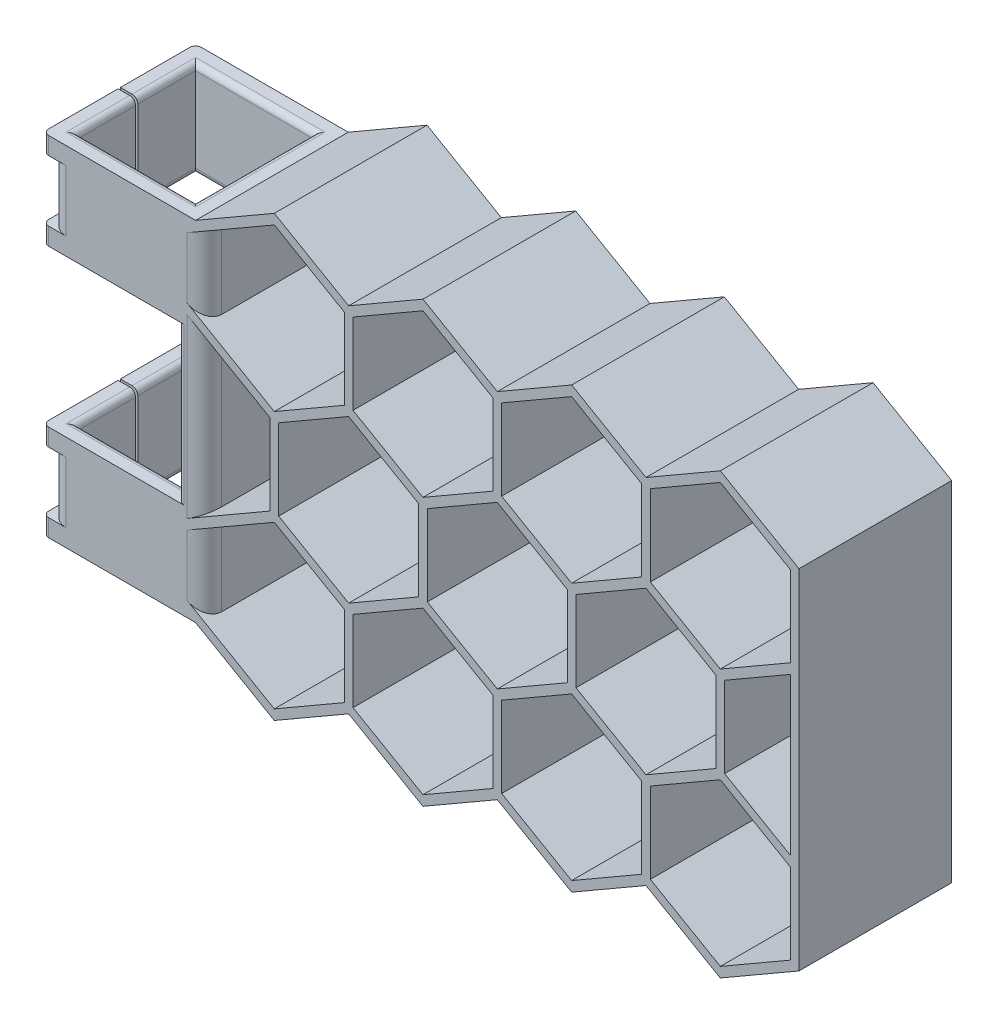
SolidWorks part; units mm, degrees
ref_plane "Front Plane" through (0, 0, 0) normal (0, 0, 1) x (1, 0, 0)
ref_plane "Top Plane" through (0, 0, 0) normal (0, 1, 0) x (1, 0, 0)
ref_plane "Right Plane" through (0, 0, 0) normal (1, 0, 0) x (0, 0, -1)
sketch "Sketch1" plane through (0, 0, 0) normal (0, 1, 0) x (1, 0, 0)
  line L1 (0, 0) -> (20.3, 0)
  line L2 (0, 0) -> (0, 20.3)
  line L3 (0, 20.3) -> (20.3, 20.3)
  line L4 (20.3, 0) -> (20.3, 20.3)
  line L5 (-3, -3) -> (23.3, -3)
  line L6 (-3, -3) -> (-3, 23.3)
  line L7 (-3, 23.3) -> (23.3, 23.3)
  line L8 (23.3, -3) -> (23.3, 23.3)
  line L9 (20.3, 20.3) -> (23.3, 20.3) construction
  line L10 (20.3, 20.3) -> (20.3, 23.3) construction
  line L11 (20.3, 23.3) -> (23.3, 23.3) construction
  line L12 (23.3, 20.3) -> (23.3, 23.3) construction
  line L13 (0, 0) -> (-3, 0) construction
  line L14 (0, 0) -> (0, -3) construction
  line L15 (0, -3) -> (-3, -3) construction
  line L16 (-3, 0) -> (-3, -3) construction
  dimension "D1" = 20.3
  dimension "D2" = 3
extrude "Tube Extrude" add sketch "Sketch1" along normal blind 60
ref_plane "tube outer plane" through (0, 0, 3) normal (0, 0, 1) x (1, 0, 0)
sketch "Sketch2" plane through (0, 0, 3) normal (0, 0, 1) x (1, 0, 0)
  line L0 (23.3, 60) -> (23.3, 0) construction
  line L1 (49.6558, 16.0825) -> (37.6029, 23.0413)
  line L2 (36.1029, 23.0413) -> (24.8, 16.5155)
  line L3 (23.3, 15.6495) -> (23.3, 0)
  line L4 (23.3, 0) -> (36.8529, -7.8248)
  line L5 (36.8529, -7.8248) -> (49.6558, -0.433)
  line L6 (50.4058, 0.866) -> (50.4058, 14.7835) construction
  line L7 (75.2615, 16.0825) -> (62.4586, 23.4743) construction
  line L8 (24.8, 0.866) -> (36.8529, -6.0927)
  line L9 (36.8529, -6.0927) -> (48.9058, 0.866)
  line L10 (48.9058, 0.866) -> (48.9058, 14.7835)
  line L11 (48.9058, 14.7835) -> (36.8529, 21.7422)
  line L12 (36.8529, 21.7422) -> (24.8, 14.7835)
  line L13 (24.8, 14.7835) -> (24.8, 0.866)
  line L14 (62.4586, 23.4743) -> (49.6558, 16.0825) construction
  line L15 (48.9058, 14.7835) -> (48.9058, 0.866) construction
  line L16 (49.6558, -0.433) -> (62.4586, -7.8248)
  line L17 (62.4586, -7.8248) -> (75.2615, -0.433)
  line L18 (76.0115, 0.866) -> (76.0115, 14.7835) construction
  line L19 (50.4058, 0.866) -> (62.4586, -6.0927)
  line L20 (62.4586, -6.0927) -> (74.5115, 0.866)
  line L21 (74.5115, 0.866) -> (74.5115, 14.7835)
  line L22 (74.5115, 14.7835) -> (62.4586, 21.7422)
  line L23 (62.4586, 21.7422) -> (50.4058, 14.7835)
  line L24 (50.4058, 14.7835) -> (50.4058, 0.866)
  line L25 (100.8673, 16.0825) -> (88.0644, 23.4743) construction
  line L26 (88.0644, 23.4743) -> (75.2615, 16.0825) construction
  line L27 (74.5115, 14.7835) -> (74.5115, 0.866) construction
  line L28 (75.2615, -0.433) -> (88.0644, -7.8248)
  line L29 (88.0644, -7.8248) -> (100.8673, -0.433)
  line L30 (101.6173, 0.866) -> (101.6173, 14.7835) construction
  line L31 (76.0115, 0.866) -> (88.0644, -6.0927)
  line L32 (88.0644, -6.0927) -> (100.1173, 0.866)
  line L33 (100.1173, 0.866) -> (100.1173, 14.7835)
  line L34 (100.1173, 14.7835) -> (88.0644, 21.7422)
  line L35 (88.0644, 21.7422) -> (76.0115, 14.7835)
  line L36 (76.0115, 14.7835) -> (76.0115, 0.866)
  line L37 (125.723, 16.5155) -> (114.4202, 23.0413)
  line L38 (112.9202, 23.0413) -> (100.8673, 16.0825) construction
  line L39 (100.1173, 14.7835) -> (100.1173, 0.866) construction
  line L40 (100.8673, -0.433) -> (113.6702, -7.8248)
  line L41 (113.6702, -7.8248) -> (127.223, 0)
  line L42 (127.223, 0) -> (127.223, 15.6495)
  line L43 (101.6173, 0.866) -> (113.6702, -6.0927)
  line L44 (113.6702, -6.0927) -> (125.723, 0.866)
  line L45 (125.723, 0.866) -> (125.723, 14.7835)
  line L46 (125.723, 14.7835) -> (113.6702, 21.7422)
  line L47 (113.6702, 21.7422) -> (101.6173, 14.7835)
  line L48 (101.6173, 14.7835) -> (101.6173, 0.866)
  line L85 (49.6558, 60.433) -> (36.8529, 67.8248)
  line L86 (36.8529, 67.8248) -> (23.3, 60)
  line L87 (23.3, 60) -> (23.3, 44.3505)
  line L88 (24.8, 43.4845) -> (36.1029, 36.9587)
  line L89 (37.6029, 36.9587) -> (49.6558, 43.9175) construction
  line L90 (75.2615, 60.433) -> (62.4586, 67.8248)
  line L91 (24.8, 45.2165) -> (36.8529, 38.2578)
  line L92 (36.8529, 38.2578) -> (48.9058, 45.2165)
  line L93 (48.9058, 45.2165) -> (48.9058, 59.134)
  line L94 (48.9058, 59.134) -> (36.8529, 66.0927)
  line L95 (36.8529, 66.0927) -> (24.8, 59.134)
  line L96 (24.8, 59.134) -> (24.8, 45.2165)
  line L97 (62.4586, 67.8248) -> (49.6558, 60.433)
  line L98 (49.6558, 43.9175) -> (62.4586, 36.5257) construction
  line L99 (62.4586, 36.5257) -> (75.2615, 43.9175) construction
  line L100 (50.4058, 45.2165) -> (62.4586, 38.2578)
  line L101 (62.4586, 38.2578) -> (74.5115, 45.2165)
  line L102 (74.5115, 45.2165) -> (74.5115, 59.134)
  line L103 (74.5115, 59.134) -> (62.4586, 66.0927)
  line L104 (62.4586, 66.0927) -> (50.4058, 59.134)
  line L105 (50.4058, 59.134) -> (50.4058, 45.2165)
  line L106 (100.8673, 60.433) -> (88.0644, 67.8248)
  line L107 (88.0644, 67.8248) -> (75.2615, 60.433)
  line L108 (75.2615, 43.9175) -> (88.0644, 36.5257) construction
  line L109 (88.0644, 36.5257) -> (100.8673, 43.9175) construction
  line L110 (76.0115, 45.2165) -> (88.0644, 38.2578)
  line L111 (88.0644, 38.2578) -> (100.1173, 45.2165)
  line L112 (100.1173, 45.2165) -> (100.1173, 59.134)
  line L113 (100.1173, 59.134) -> (88.0644, 66.0927)
  line L114 (88.0644, 66.0927) -> (76.0115, 59.134)
  line L115 (76.0115, 59.134) -> (76.0115, 45.2165)
  line L116 (127.223, 60) -> (113.6702, 67.8248)
  line L117 (113.6702, 67.8248) -> (100.8673, 60.433)
  line L118 (100.8673, 43.9175) -> (113.6702, 36.5257) construction
  line L119 (114.4202, 36.9587) -> (125.723, 43.4845)
  line L120 (127.223, 44.3505) -> (127.223, 60)
  line L121 (101.6173, 45.2165) -> (113.6702, 38.2578)
  line L122 (113.6702, 38.2578) -> (125.723, 45.2165)
  line L123 (125.723, 45.2165) -> (125.723, 59.134)
  line L124 (125.723, 59.134) -> (113.6702, 66.0927)
  line L125 (113.6702, 66.0927) -> (101.6173, 59.134)
  line L126 (101.6173, 59.134) -> (101.6173, 45.2165)
  line L127 (50.4058, 45.2165) -> (50.4058, 59.134) construction
  line L128 (48.9058, 59.134) -> (48.9058, 45.2165) construction
  line L129 (76.0115, 45.2165) -> (76.0115, 59.134) construction
  line L130 (74.5115, 59.134) -> (74.5115, 45.2165) construction
  line L131 (101.6173, 45.2165) -> (101.6173, 59.134) construction
  line L132 (100.1173, 59.134) -> (100.1173, 45.2165) construction
  line L133 (114.4202, 23.0413) -> (114.4202, 22.1752) construction
  line L134 (62.4586, 21.7422) -> (75.2615, 14.3505) construction
  line L135 (36.8529, 21.7422) -> (49.6558, 14.3505) construction
  line L136 (49.6558, 14.3505) -> (62.4586, 21.7422) construction
  line L137 (63.2086, 23.0413) -> (63.2086, 36.9587) construction
  line L138 (62.4586, 38.2578) -> (49.6558, 45.6495) construction
  line L139 (49.6558, 45.6495) -> (36.8529, 38.2578) construction
  line L140 (36.1029, 36.9587) -> (36.1029, 23.0413)
  line L141 (49.6558, 16.0825) -> (61.7086, 23.0413)
  line L142 (61.7086, 23.0413) -> (61.7086, 36.9587)
  line L143 (61.7086, 36.9587) -> (49.6558, 43.9175)
  line L144 (49.6558, 43.9175) -> (37.6029, 36.9587)
  line L145 (37.6029, 36.9587) -> (37.6029, 23.0413)
  line L146 (37.6029, 23.0413) -> (49.6558, 16.0825)
  line L147 (75.2615, 14.3505) -> (88.0644, 21.7422) construction
  line L148 (88.8144, 23.0413) -> (88.8144, 36.9587) construction
  line L149 (88.0644, 38.2578) -> (75.2615, 45.6495) construction
  line L150 (75.2615, 45.6495) -> (62.4586, 38.2578) construction
  line L151 (61.7086, 36.9587) -> (61.7086, 23.0413) construction
  line L152 (75.2615, 16.0825) -> (87.3144, 23.0413)
  line L153 (87.3144, 23.0413) -> (87.3144, 36.9587)
  line L154 (87.3144, 36.9587) -> (75.2615, 43.9175)
  line L155 (75.2615, 43.9175) -> (63.2086, 36.9587)
  line L156 (63.2086, 36.9587) -> (63.2086, 23.0413)
  line L157 (63.2086, 23.0413) -> (75.2615, 16.0825)
  line L158 (88.0644, 21.7422) -> (100.8673, 14.3505) construction
  line L159 (100.8673, 14.3505) -> (114.4202, 22.1752) construction
  line L160 (114.4202, 23.0413) -> (114.4202, 36.9587)
  line L161 (113.6702, 38.2578) -> (100.8673, 45.6495) construction
  line L162 (100.8673, 45.6495) -> (88.0644, 38.2578) construction
  line L163 (87.3144, 36.9587) -> (87.3144, 23.0413) construction
  line L164 (100.8673, 16.0825) -> (112.9202, 23.0413)
  line L165 (112.9202, 23.0413) -> (112.9202, 36.9587)
  line L166 (112.9202, 36.9587) -> (100.8673, 43.9175)
  line L167 (100.8673, 43.9175) -> (88.8144, 36.9587)
  line L168 (88.8144, 36.9587) -> (88.8144, 23.0413)
  line L169 (88.8144, 23.0413) -> (100.8673, 16.0825)
  line L170 (114.4202, 36.9587) -> (113.6702, 36.5257)
  line L171 (127.223, 44.3505) -> (127.223, 15.6495)
  line L172 (125.723, 16.5155) -> (125.723, 43.4845)
  line L173 (23.3, 15.6495) -> (23.3, 44.3505)
  line L174 (24.8, 16.5155) -> (24.8, 43.4845)
  line L180 (-3, 60) -> (23.3, 60) construction
  circle A0 centre (36.8529, 7.8248) radius 13.5529 construction
  circle A1 centre (36.8529, 7.8248) radius 12.0529 construction
  circle A2 centre (62.4586, 7.8248) radius 13.5529 construction
  circle A3 centre (62.4586, 7.8248) radius 12.0529 construction
  circle A4 centre (88.0644, 7.8248) radius 13.5529 construction
  circle A5 centre (88.0644, 7.8248) radius 12.0529 construction
  circle A6 centre (113.6702, 7.8248) radius 13.5529 construction
  circle A7 centre (113.6702, 7.8248) radius 12.0529 construction
  circle A8 centre (49.6558, 30) radius 13.5529 construction
  circle A9 centre (49.6558, 30) radius 12.0529 construction
  circle A10 centre (75.2615, 30) radius 13.5529 construction
  circle A11 centre (75.2615, 30) radius 12.0529 construction
  circle A12 centre (100.8673, 30) radius 13.5529 construction
  circle A13 centre (100.8673, 30) radius 12.0529 construction
  circle A14 centre (36.8529, 52.1752) radius 13.5529 construction
  circle A15 centre (36.8529, 52.1752) radius 12.0529 construction
  circle A16 centre (62.4586, 52.1752) radius 13.5529 construction
  circle A17 centre (62.4586, 52.1752) radius 12.0529 construction
  circle A18 centre (88.0644, 52.1752) radius 13.5529 construction
  circle A19 centre (88.0644, 52.1752) radius 12.0529 construction
  circle A20 centre (113.6702, 52.1752) radius 13.5529 construction
  circle A21 centre (113.6702, 52.1752) radius 12.0529 construction
  dimension "D1" = 0
  dimension "D2" = 1.5
  dimension "D3" = 4
  dimension "D5" = 2
  dimension "D4" = 3
extrude "Hex Extrude" add sketch "Sketch2" against normal up to surface (26.3 mm away) contours L12 L13 L8 L9 L10 L11 | L23 L24 L19 L20 L21 L22 | L144 L145 L1 L141 L142 L143 | L174 L2 L140 L88 | L95 L96 L91 L92 L93 L94 | L104 L105 L100 L101 L102 L103 | L156 L157 L152 L153 L154 L155 | L35 L36 L31 L32 L33 L34 | L168 L169 L164 L165 L166 L167 | L114 L115 L110 L111 L112 L113 | L125 L126 L121 L122 L123 L124 | L47 L48 L43 L44 L45 L46 | L37 L172 L119 L160 | L16 L17 L28 L29 L40 L41 L42 L171 L120 L116 L117 L106 L107 L90 L97 L85 L86 L87 L173 L3 L4 L5
sketch "Sketch3" plane through (0, 0, 3) normal (0, 0, 1) x (1, 0, 0)
  line L0 (-3, 60) -> (-3, 0) construction
  line L1 (20.3, 43.4845) -> (-3, 43.4845)
  line L2 (20.3, 43.4845) -> (20.3, 16.5155)
  line L3 (20.3, 16.5155) -> (-3, 16.5155)
  line L4 (-3, 43.4845) -> (-3, 16.5155)
  line L5 (20.3, 43.4845) -> (24.8, 43.4845) construction
  line L6 (20.3, 16.5155) -> (24.8, 16.5155) construction
extrude "Tube Center Cut" cut sketch "Sketch3" against normal through all both and the other way through all
ref_plane "Plane1" through (-3, 0, 0) normal (-1, 0, 0) x (0, 0, 1)
sketch "Sketch4" plane through (-3, 0, 0) normal (-1, 0, 0) x (0, 0, 1)
  line L0 (-10.15, 60) -> (-10.35, 60)
  line L1 (-23.3, 60) -> (3, 60) construction
  line L2 (-10.35, 60) -> (-10.35, 0)
  line L3 (-23.3, 0) -> (3, 0) construction
  line L4 (-10.35, 0) -> (-10.15, 0)
  line L5 (-10.15, 0) -> (-9.95, 0)
  line L6 (-9.95, 0) -> (-9.95, 60)
  line L7 (-9.95, 60) -> (-10.15, 60)
  dimension "D1" = 0.2
extrude "Cut-Extrude1" cut sketch "Sketch4" against normal up to next
sketch "Sketch5" plane through (0, 0, 3) normal (0, 0, 1) x (1, 0, 0)
  line L0 (-3, 7.1225) -> (-3, -7.1225) construction
  line L1 (-3, 57) -> (-2, 57)
  line L2 (-3, 57) -> (-3, 46.4845)
  line L3 (-3, 46.4845) -> (-2, 46.4845)
  line L4 (-2, 57) -> (-2, 46.4845)
  line L5 (20.3, 30) -> (-9.7, 30) construction
  line L6 (20.3, 43.4845) -> (20.3, 16.5155) construction
  line L7 (-2, 57) -> (-2, 60) construction
  line L8 (-3, 60) -> (23.3, 60) construction
  line L9 (-2, 46.4845) -> (-2, 43.4845) construction
  line L10 (-3, 43.4845) -> (20.3, 43.4845) construction
  line L11 (-2, 3) -> (-2, 13.5155)
  line L12 (-3, 13.5155) -> (-2, 13.5155)
  line L13 (-3, 3) -> (-3, 13.5155)
  line L14 (-3, 3) -> (-2, 3)
  dimension "D1" = 30
  dimension "D2" = 3
  dimension "D3" = 1
extrude "Cut-Extrude2" cut sketch "Sketch5" against normal through all
fillet "Fillet1" radius 3 10 edges at (24.8, 7.8248, -23.3) (24.8, 7.8248, 3) (24.8, 52.1752, -23.3) (24.8, 52.1752, 3) (-2, 51.7422, -23.3) (-2, 51.7422, 3) (-2, 8.2578, 3) (-2, 8.2578, -23.3) (24.8, 30, -23.3) (24.8, 30, 3)
fillet "Fillet2" radius 1 28 edges at (20.3, 30, -23.3) (20.3, 30, 3) (10.15, 16.5155, -20.3) (0, 16.5155, -15.325) (0, 16.5155, -4.975) (10.15, 16.5155, 0) (10.15, 0, -20.3) (0, 0, -15.325) (0, 0, -4.975) (20.3, 0, -10.15) (10.15, 0, 0) (10.15, 43.4845, 0) (0, 43.4845, -4.975) (0, 43.4845, -15.325) (10.15, 43.4845, -20.3) (0, 60, -4.975) (0, 60, -15.325) (10.15, 60, -20.3) (10.15, 60, 0) (20.3, 60, -10.15) (-3, 44.9845, -23.3) (-3, 58.5, -23.3) (-3, 44.9845, 3) (-3, 58.5, 3) (-3, 1.5, 3) (-3, 15.0155, 3) (-3, 1.5, -23.3) (-3, 15.0155, -23.3)
